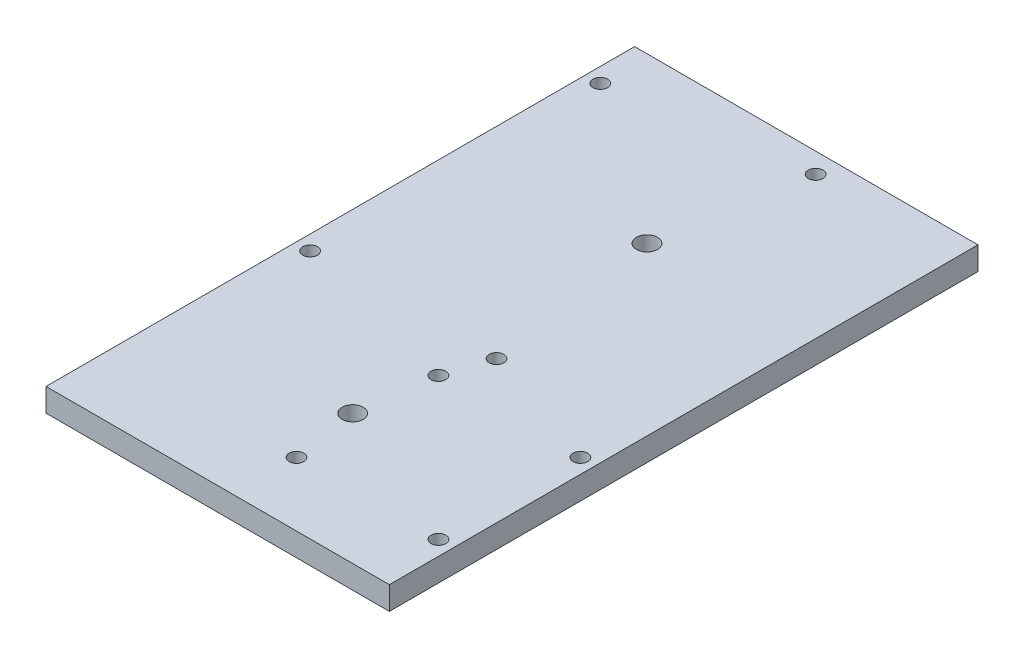
SolidWorks part; units mm, degrees
material "Melamine resin"
ref_plane "Front Plane" through (0, 0, 0) normal (0, 0, 1) x (1, 0, 0)
ref_plane "Top Plane" through (0, 0, 0) normal (0, 1, 0) x (1, 0, 0)
ref_plane "Right Plane" through (0, 0, 0) normal (1, 0, 0) x (0, 0, -1)
sketch "Sketch2" plane through (0, 0, 0) normal (0, 1, 0) x (1, 0, 0)
  line L1 (0, 0) -> (88.9, 0)
  line L2 (0, 0) -> (0, 152.4)
  line L3 (0, 152.4) -> (88.9, 152.4)
  line L10 (88.9, 152.4) -> (88.9, 0)
  dimension "D1" = 152.4
  dimension "D2" = 88.9
extrude "Boss-Extrude1" add sketch "Sketch2" along normal blind 5.9944 contours L3 L10 L1 L2
sketch "Sketch3" plane through (0, 5.9944, 0) normal (0, 1, 0) x (1, 0, 0)
  line L0 (0, 0) -> (0, 152.4) construction
  line L2 (0, 152.4) -> (88.9, 152.4) construction
  line L3 (85.09, 53.2638) -> (48.3362, 53.2638) construction
  line L4 (85.09, 53.2638) -> (85.09, 16.51) construction
  line L5 (85.09, 16.51) -> (48.3362, 16.51) construction
  line L6 (48.3362, 53.2638) -> (48.3362, 16.51) construction
  line L8 (0, 0) -> (88.9, 0) construction
  line L9 (0, 0) -> (88.9, 0) construction
  line L10 (88.9, 152.4) -> (88.9, 0) construction
  circle A5 centre (52.07, 147.193) radius 1.905
  circle A6 centre (3.81, 139.7) radius 1.905
  circle A7 centre (3.81, 64.5668) radius 1.905
  circle A8 centre (52.07, 64.5668) radius 1.905
  circle A9 centre (48.3362, 53.2638) radius 1.905
  circle A10 centre (85.09, 53.2638) radius 1.905
  circle A11 centre (48.3362, 16.51) radius 1.905
  circle A12 centre (85.09, 16.51) radius 1.905
  point P0 (52.07, 147.193)
  point P1 (3.81, 139.7)
  point P2 (3.81, 64.5668)
  point P3 (52.07, 64.5668)
  point P21 (85.09, 53.2638)
  point P22 (85.09, 16.51)
  point P23 (48.3362, 53.2638)
  point P24 (48.3362, 16.51)
  dimension "D4" = 3.81
  dimension "D5" = 3.81
  dimension "D6" = 3.81
  dimension "D7" = 3.81
  dimension "D9" = 3.81
  dimension "D16" = 3.81
  dimension "D17" = 3.81
  dimension "D18" = 3.81
  dimension "D19" = 3.81
  dimension "D1" = 48.26
  dimension "D2" = 82.6262
  dimension "D3" = 75.1332
  dimension "D8" = 12.7
  dimension "D10" = 36.7538
  dimension "D11" = 36.7538
  dimension "D12" = 16.51
  dimension "D13" = 3.81
  dimension "D14" = 48.3362
  dimension "D15" = 16.51
extrude "Cut-Extrude1" cut sketch "Sketch3" against normal through all both and the other way through all contours A6 | A5 | A8 | A7 | A11 | A9 | A10 | A12
sketch "Sketch4" plane through (0, 5.9944, 0) normal (0, 1, 0) x (1, 0, 0)
  line L0 (0, 0) -> (0, 152.4) construction
  line L1 (0, 0) -> (88.9, 0) construction
  circle A0 centre (45.72, 109.8713) radius 2.7305
  circle A1 centre (45.72, 33.6713) radius 2.7305
  dimension "D3" = 5.461
  dimension "D4" = 5.461
  dimension "D1" = 76.2
  dimension "D2" = 45.72
  dimension "D5" = 33.6713
extrude "Cut-Extrude2" cut sketch "Sketch4" against normal through all both
equation "\"threaded_insert_hole\"=0.1472"
equation "\"th\"=1.25249"
